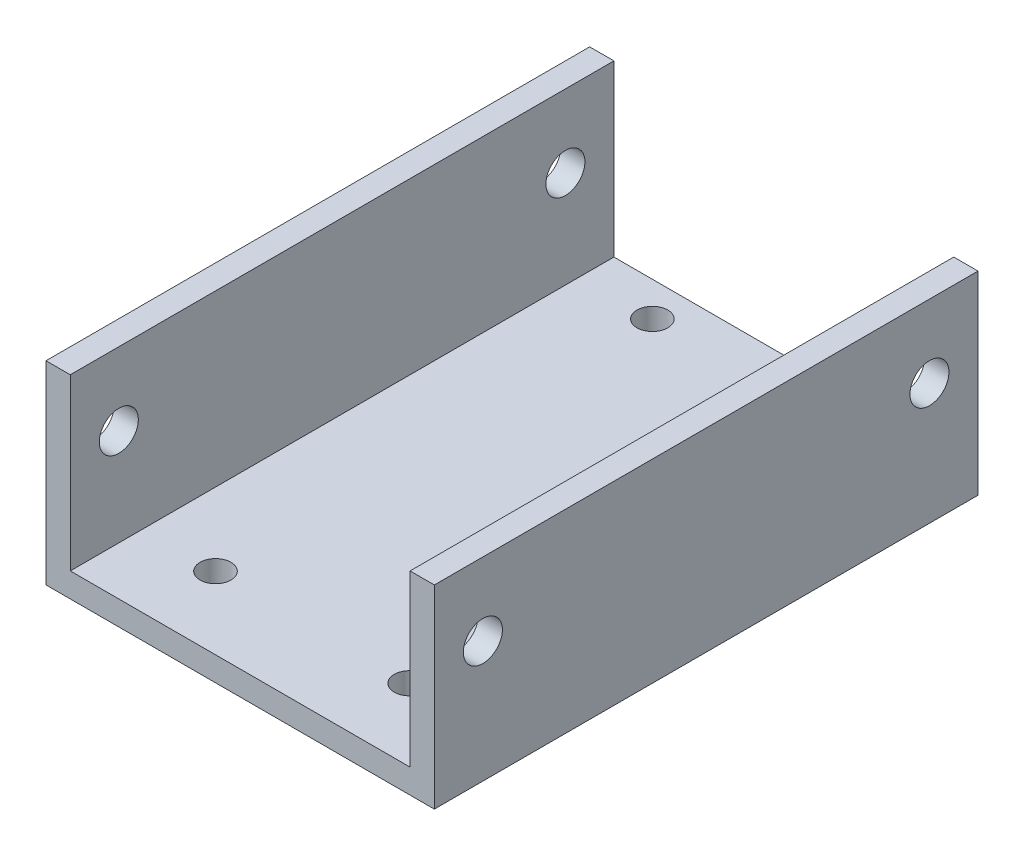
SolidWorks part; units mm, degrees
material "6063-T6"
ref_plane "Front" through (0, 0, 0) normal (0, 0, 1) x (1, 0, 0)
ref_plane "Top" through (0, 0, 0) normal (0, 1, 0) x (1, 0, 0)
ref_plane "Right" through (0, 0, 0) normal (1, 0, 0) x (0, 0, -1)
sketch "Sketch1" plane through (0, 0, 0) normal (0, 0, 1) x (1, 0, 0)
  line L0 (47.625, 3.175) -> (47.625, 25.4)
  line L1 (0, 0) -> (50.8, 0)
  line L2 (0, 0) -> (0, 25.4)
  line L4 (50.8, 0) -> (50.8, 25.4)
  line L5 (3.175, 3.175) -> (47.625, 3.175)
  line L6 (3.175, 3.175) -> (3.175, 25.4)
  line L7 (50.8, 25.4) -> (47.625, 25.4)
  line L8 (0, 25.4) -> (3.175, 25.4)
  dimension "D1" = 25.4
  dimension "D2" = 50.8
  dimension "D3" = 3.175
extrude "Boss-Extrude1" add sketch "Sketch1" along normal blind 71.12
sketch "Sketch2" plane through (0, 3.175, 0) normal (0, 1, 0) x (1, 0, 0)
  circle A0 centre (38.1, -4.4975) radius 2.0193 construction
  circle A1 centre (38.1, -4.4975) radius 2.0193
  circle A2 centre (38.1, -61.6475) radius 2.0193 construction
  circle A3 centre (38.1, -61.6475) radius 2.0193
  circle A4 centre (12.7, -4.4975) radius 2.0193 construction
  circle A5 centre (12.7, -4.4975) radius 2.0193
  circle A6 centre (12.7, -61.6475) radius 2.0193 construction
  circle A7 centre (12.7, -61.6475) radius 2.0193
extrude "Cut-Extrude1" cut sketch "Sketch2" against normal up to next
sketch "Sketch3" plane through (50.8, 0, 0) normal (1, 0, 0) x (0, 0, -1)
  circle A0 centre (-6.35, 15.875) radius 2.5527 construction
  circle A1 centre (-6.35, 15.875) radius 2.5527
  circle A2 centre (-64.77, 15.875) radius 2.5527 construction
  circle A3 centre (-64.77, 15.875) radius 2.5527
extrude "Cut-Extrude2" cut sketch "Sketch3" against normal through all
